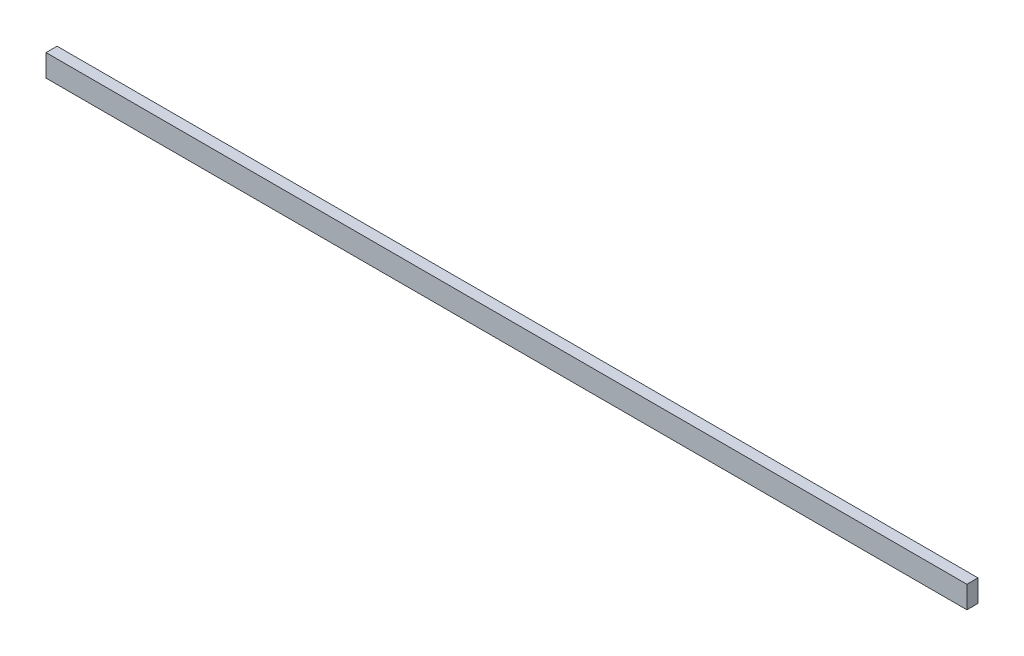
SolidWorks part; units mm, degrees
ref_plane "Front Plane" through (0, 0, 0) normal (0, 0, 1) x (1, 0, 0)
ref_plane "Top Plane" through (0, 0, 0) normal (0, 1, 0) x (1, 0, 0)
ref_plane "Right Plane" through (0, 0, 0) normal (1, 0, 0) x (0, 0, -1)
sketch "Sketch1" plane through (0, 0, 0) normal (0, 0, 1) x (1, 0, 0)
  line L1 (-208, 5) -> (208, 5)
  line L2 (-208, 5) -> (-208, -5)
  line L3 (-208, -5) -> (208, -5)
  line L4 (208, 5) -> (208, -5)
  line L5 (-208, 5) -> (208, -5) construction
  line L6 (-208, -5) -> (208, 5) construction
  point P0 (0, 0)
  dimension "D1" = 10
  dimension "D2" = 416
extrude "Boss-Extrude1" add sketch "Sketch1" along normal blind 5
